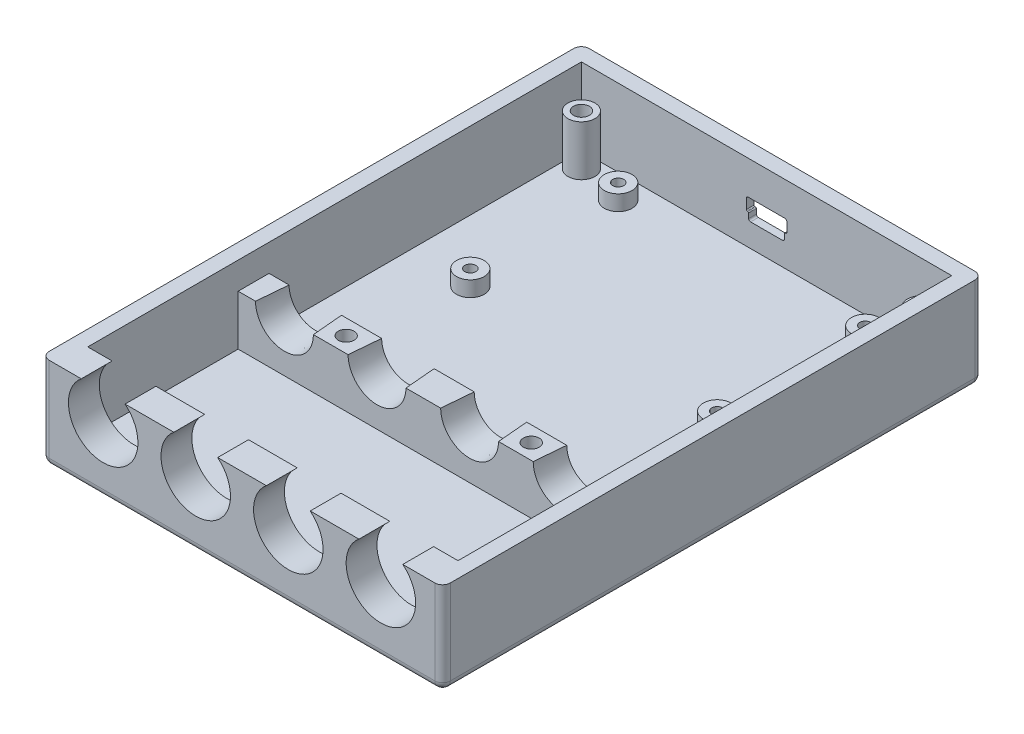
SolidWorks part; units mm, degrees
ref_plane "Front Plane" through (0, 0, 0) normal (0, 0, 1) x (1, 0, 0)
ref_plane "Top Plane" through (0, 0, 0) normal (0, 1, 0) x (1, 0, 0)
ref_plane "Right Plane" through (0, 0, 0) normal (1, 0, 0) x (0, 0, -1)
sketch "Sketch1" plane through (0, 0, 0) normal (0, 1, 0) x (1, 0, 0)
  line L1 (-41.275, -55.5625) -> (41.275, -55.5625)
  line L2 (-41.275, -55.5625) -> (-41.275, 55.5625)
  line L3 (-41.275, 55.5625) -> (41.275, 55.5625)
  line L4 (41.275, -55.5625) -> (41.275, 55.5625)
  line L5 (-41.275, -55.5625) -> (41.275, 55.5625) construction
  line L6 (-41.275, 55.5625) -> (41.275, -55.5625) construction
  point P0 (0, 0)
  dimension "D1" = 82.55
  dimension "D2" = 111.125
extrude "Boss-Extrude1" add sketch "Sketch1" along normal blind 19.05
sketch "Sketch11" plane through (0, 0, 55.5625) normal (0, 0, 1) x (1, 0, 0)
  line L0 (0, 19.05) -> (0, 6.35) construction
  line L1 (-41.275, 19.05) -> (41.275, 19.05) construction
  line L2 (-41.275, 6.35) -> (41.275, 6.35) construction
  line L3 (-41.275, 19.05) -> (-41.275, 0) construction
  line L4 (41.275, 19.05) -> (41.275, 0) construction
  circle A0 centre (-28.575, 13.5001) radius 7.1501
  circle A1 centre (-9.525, 13.5001) radius 7.1501
  circle A2 centre (9.525, 13.5001) radius 7.1501
  circle A3 centre (28.575, 13.5001) radius 7.1501
  point P11 (-38.1, 6.35)
  point P12 (-28.575, 6.35)
  point P13 (-9.525, 6.35)
  point P14 (9.525, 6.35)
  point P15 (28.575, 6.35)
  point P16 (38.1, 6.35)
  point P17 (-28.575, 20.6502)
  point P18 (-9.525, 20.6502)
  point P19 (9.525, 20.6502)
  point P20 (28.575, 20.6502)
  dimension "D1" = 12.7
  dimension "D2" = 3.175
  dimension "D3" = 9.525
  dimension "D4" = 19.05
  dimension "D5" = 19.05
  dimension "D6" = 19.05
  dimension "D7" = 3.175
  dimension "D8" = 9.525
  dimension "D9" = 14.3002
  dimension "D10" = 14.3002
  dimension "D11" = 14.3002
  dimension "D12" = 14.3002
sketch "Sketch14" plane through (0, 19.05, 0) normal (0, 1, 0) x (-1, 0, 0)
  line L0 (0, 0) -> (0, -1.5875) construction
  line L3 (38.1, 49.2125) -> (-38.1, 49.2125)
  line L4 (38.1, 49.2125) -> (38.1, -52.3875)
  line L5 (38.1, -52.3875) -> (-38.1, -52.3875)
  line L6 (-38.1, 49.2125) -> (-38.1, -52.3875)
  line L7 (38.1, 49.2125) -> (-38.1, -52.3875) construction
  line L8 (38.1, -52.3875) -> (-38.1, 49.2125) construction
  dimension "D1" = 1.5875
  dimension "D2" = 101.6
  dimension "D3" = 76.2
extrude "Cut-Extrude3" cut sketch "Sketch14" against normal offset from surface (15.875 mm away) 3.175 up to face at (0, 0, 0)
extrude "Cut-Extrude4" cut sketch "Sketch11" against normal up to next
sketch "Sketch16" plane through (0, 0, 49.2125) normal (0, 0, -1) x (-1, 0, 0)
  point P0 (28.575, 13.5001)
  point P1 (-28.575, 13.5001)
sketch3d "ControllerCenter"
sketch "Sketch17" plane through (0, 3.175, 0) normal (0, 1, 0) x (-1, 0, 0)
  line L0 (0, 49.2125) -> (0, 18.2562) construction
  line L1 (5.0169, 49.2125) -> (-5.0169, 49.2125) construction
  line L2 (38.1, 18.2562) -> (-38.1, 18.2562)
  line L3 (38.1, 18.2562) -> (38.1, 11.9062)
  line L4 (-38.1, 18.2562) -> (-38.1, 11.9062)
  line L5 (38.1, 11.9062) -> (-38.1, 11.9062)
  line L6 (38.1, -52.3875) -> (38.1, 49.2125) construction
  line L7 (-38.1, 49.2125) -> (-38.1, -52.3875) construction
  line L8 (0, -52.3875) -> (0, 11.9062) construction
  line L9 (-38.1, -52.3875) -> (38.1, -52.3875) construction
  circle A0 centre (34.925, -49.2125) radius 2.7781
  circle A1 centre (-34.925, -49.2125) radius 2.7781
  dimension "D5" = 5.5562
  dimension "D1" = 30.9562
  dimension "D2" = 6.35
  dimension "D3" = 3.175
  dimension "D4" = 3.175
extrude "Boss-Extrude4" add sketch "Sketch17" along normal up to surface (10.3251 mm away)
sketch "Sketch18" plane through (0, 0, 18.2562) normal (0, 0, 1) x (1, 0, 0)
  line L0 (-38.1, 13.5001) -> (38.1, 13.5001) construction
  circle A0 centre (-28.575, 13.5001) radius 5.9531
  circle A1 centre (-9.525, 13.5001) radius 5.9531
  circle A2 centre (9.525, 13.5001) radius 5.9531
  circle A3 centre (28.575, 13.5001) radius 5.9531
  point P0 (-28.575, 13.5001)
  point P1 (-9.525, 13.5001)
  point P4 (9.525, 13.5001)
  point P5 (28.575, 13.5001)
  dimension "D6" = 11.9062
  dimension "D7" = 11.9062
  dimension "D8" = 11.9062
  dimension "D9" = 11.9062
  dimension "D1" = 9.525
  dimension "D2" = 19.05
  dimension "D3" = 19.05
  dimension "D4" = 19.05
  dimension "D5" = 9.525
extrude "Cut-Extrude5" cut sketch "Sketch18" against normal up to next (6.35 mm away) draft 5
sketch "Sketch19" plane through (0, 3.175, 0) normal (0, 1, 0) x (-1, 0, 0)
  line L0 (38.1, -20.2406) -> (-38.1, -20.2406) construction
  line L1 (38.1, -52.3875) -> (38.1, 11.9062) construction
  line L2 (-38.1, 11.9062) -> (-38.1, -52.3875) construction
  line L3 (25.4, -52.3875) -> (25.4, 11.9062) construction
  line L4 (-38.1, -52.3875) -> (38.1, -52.3875) construction
  line L5 (-38.1, 11.9062) -> (38.1, 11.9062) construction
  line L6 (-25.4, -52.3875) -> (-25.4, 11.9062) construction
  line L7 (-38.1, -52.3875) -> (38.1, -52.3875) construction
  circle A0 centre (25.5143, -47.371) radius 2.8575
  circle A1 centre (-25.4, -47.3075) radius 2.8575
  circle A2 centre (25.4, -16.8275) radius 2.8575
  circle A3 centre (-25.4, -16.8275) radius 2.8575
  point P6 (25.4, -20.2406)
  point P7 (-25.4, -20.2406)
  point P18 (25.4, -47.3075)
  point P19 (-25.4, -47.3075)
  point P20 (25.4, -16.8275)
  point P21 (-25.4, -16.8275)
  point P30 (25.5143, -47.3075)
  point P31 (25.4, -47.371)
  dimension "D7" = 5.715
  dimension "D8" = 5.715
  dimension "D9" = 5.715
  dimension "D10" = 5.715
  dimension "D1" = 50.8
  dimension "D2" = 12.7
  dimension "D3" = 5.08
  dimension "D4" = 5.08
  dimension "D5" = 30.48
  dimension "D6" = 30.48
  dimension "D11" = 0.1143
  dimension "D12" = 0.0635
sketch "Sketch21" plane through (0, 0, -55.5625) normal (0, 0, -1) x (-1, 0, 0)
  line L0 (0, 19.05) -> (0, 0) construction
  line L1 (-41.275, 19.05) -> (41.275, 19.05) construction
  line L2 (0, 7.9375) -> (3.683, 7.9375) construction
  line L3 (-3.683, 7.9375) -> (-3.683, 9.525)
  line L4 (-3.683, 7.9375) -> (3.683, 7.9375)
  line L5 (-3.683, 9.525) -> (-4.1672, 9.525)
  line L6 (4.1672, 9.525) -> (4.1672, 12.1047)
  line L7 (-4.1672, 12.1047) -> (4.1672, 12.1047)
  line L8 (-4.1672, 9.525) -> (-4.1672, 12.1047)
  line L9 (-4.1672, 12.1047) -> (4.1672, 7.9375) construction
  line L10 (-4.1672, 7.9375) -> (4.1672, 12.1047) construction
  line L14 (3.683, 7.9375) -> (3.683, 9.525)
  line L15 (3.683, 9.525) -> (4.1672, 9.525)
  point P11 (0, 12.1047)
  point P13 (0, 10.0211)
  dimension "D1" = 4.1672
  dimension "D2" = 3.683
  dimension "D3" = 1.5875
  dimension "D4" = 2.5797
extrude "Cut-Extrude7" cut sketch "Sketch21" against normal up to next
fillet "Fillet6" radius 1.5875 8 edges at (-41.275, 0, 0) (-41.275, 9.525, -55.5625) (0, 0, -55.5625) (41.275, 9.525, -55.5625) (41.275, 0, 0) (0, 0, 55.5625) (41.275, 9.525, 55.5625) (-41.275, 9.525, 55.5625)
sketch "Sketch25" plane through (0, 0, -52.3875) normal (0, 0, 1) x (1, 0, 0)
  line L0 (-5.2218, 3.175) -> (-5.2218, 19.05) construction
  line L1 (38.1, 3.175) -> (-38.1, 3.175) construction
  line L2 (38.1, 19.05) -> (-38.1, 19.05) construction
  point P4 (-5.2218, 6.35)
  point P7 (-5.2218, 7.9375)
  dimension "D1" = 3.175
  dimension "D2" = 1.5875
sketch3d "BoardTop"
extrude "Boss-Extrude8" add sketch "Sketch19" along normal offset from surface (3.175 mm away) 1.5875
sketch "HoleLocations" plane through (0, 13.5001, 0) normal (0, 1, 0) x (-1, 0, 0)
  point P0 (19.05, 15.0812)
  point P1 (-19.05, 15.0812)
  point P2 (34.925, -49.2125)
  point P3 (-34.925, -49.2125)
sketch "HoleLocationsUnder" plane through (0, 0, 0) normal (0, -1, 0) x (1, 0, 0)
  point P0 (-19.05, 15.0812)
  point P1 (19.05, 15.0812)
hole_wizard "CBORE for #4 Pan Head Machine Screw3" positions "Sketch34" profile "Sketch35" counterbore size "#4" standard "Ansi Inch" end condition through all
sketch "Sketch34" plane through (0, 0, 0) normal (0, -1, 0) x (1, 0, 0)
  point P0 (-19.05, 15.0812)
  point P4 (19.05, 15.0812)
  point P7 (-34.925, -49.2125)
  point P10 (34.925, -49.2125)
sketch "Sketch35" plane through (-19.05, 0, 15.0812) normal (1, 0, 0) x (0, 0, -1)
  line L0 (0, 0) -> (0, 19.05)
  line L1 (0, 19.05) -> (1.6319, 19.05)
  line L3 (1.6319, 19.05) -> (1.632, 2.032)
  line L4 (1.632, 2.032) -> (3.175, 2.032)
  line L5 (3.175, 2.032) -> (3.175, 0)
  line L7 (3.175, 0) -> (0, 0)
  line L11 (0, -6.35) -> (0, 107.95) construction
  dimension "Thru Hole Dia." = 3.2639
  dimension "Thru Hole Depth" = 19.05
  dimension "C'Bore Dia." = 6.35
  dimension "C'Bore Depth" = 2.032
hole_wizard "#4-40 Tapped Hole1" positions "Sketch37" profile "Sketch38" tap size "#4-40" standard "Ansi Inch"
sketch "Sketch37" plane through (0, 6.35, 0) normal (0, 1, 0) x (-1, 0, 0)
  point P0 (25.5143, -47.371)
  point P4 (25.4, -16.8275)
  point P7 (-25.4, -16.8275)
  point P10 (-25.4, -47.3075)
sketch "Sketch38" plane through (-25.5143, 6.35, -47.371) normal (1, 0, 0) x (0, 0, 1)
  line L0 (0, 0) -> (0, 5.4544)
  line L1 (0, 5.4544) -> (1.1303, 4.7752)
  line L2 (1.1303, 4.7752) -> (1.1303, 0)
  line L5 (1.1303, 0) -> (0, 0)
  line L10 (0, 5.4544) -> (-1.1303, 4.7752) construction
  line L11 (0, -6.35) -> (0, 107.95) construction
  dimension "Tap Drill Dia." = 2.2606
  dimension "Tap Drill Depth" = 4.7752
  dimension "Drill Angle" = 118
cosmetic thread "Hole Thread1" parameters "D1"=4.7752, "D2"=2.8448
cosmetic thread "Hole Thread2" parameters "D1"=4.7752, "D2"=2.8448
cosmetic thread "Hole Thread3" parameters "D1"=4.7752, "D2"=2.8448
cosmetic thread "Hole Thread4" parameters "D1"=4.7752, "D2"=2.8448
sketch "Sketch39" plane through (0, 0, -55.5625) normal (0, 0, -1) x (-1, 0, 0)
  line L0 (-4.1672, 12.1047) -> (4.1672, 7.9375) construction
  line L1 (4.1672, 12.1047) -> (-4.1672, 7.9375) construction
  line L3 (-8.7312, 2.8773) -> (8.7313, 2.8773)
  line L4 (-8.7312, 2.8773) -> (-8.7312, 17.1648)
  line L5 (-8.7312, 17.1648) -> (8.7313, 17.1648)
  line L6 (8.7313, 2.8773) -> (8.7313, 17.1648)
  line L7 (-8.7312, 2.8773) -> (8.7313, 17.1648) construction
  line L8 (-8.7312, 17.1648) -> (8.7313, 2.8773) construction
  point P6 (0, 10.0211)
  dimension "D1" = 14.2875
  dimension "D2" = 17.4625
extrude "Cut-Extrude8" cut sketch "Sketch39" against normal blind 1.5875
fillet "Fillet7" radius 0.7937 4 edges at (8.7312, 2.8773, -54.7688) (-8.7313, 2.8773, -54.7688) (-8.7313, 17.1648, -54.7688) (8.7312, 17.1648, -54.7688)
fillet "Fillet8" radius 0.1984 4 edges at (-4.1672, 9.525, -53.1813) (-3.683, 9.525, -53.1813) (4.1672, 9.525, -53.1813) (3.683, 9.525, -53.1813)
fillet "Fillet9" radius 0.3969 4 edges at (3.683, 7.9375, -53.1813) (-3.683, 7.9375, -53.1813) (-4.1672, 12.1047, -53.1813) (4.1672, 12.1047, -53.1813)
